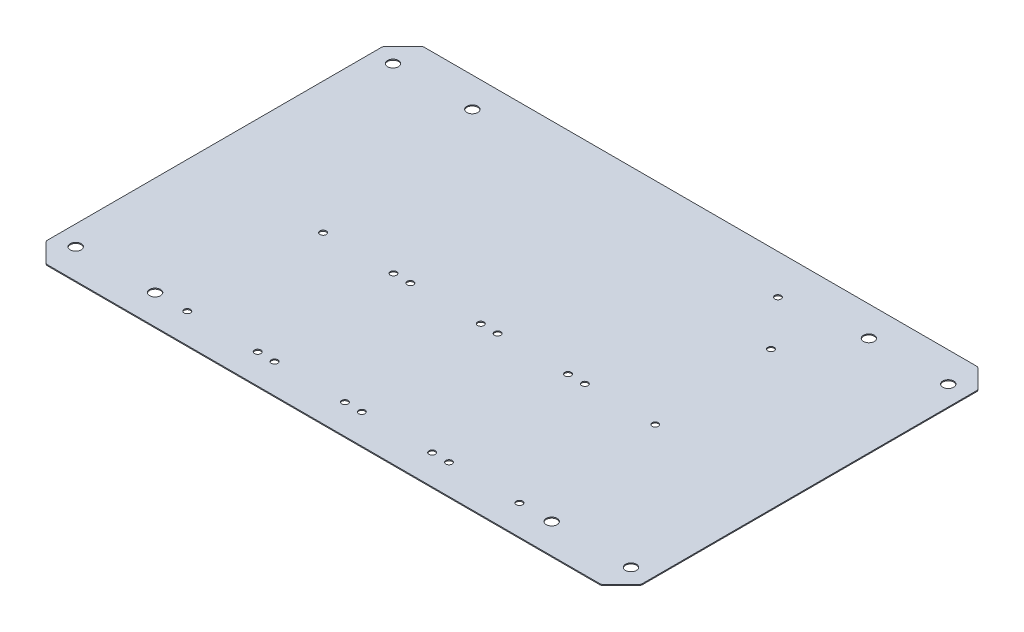
SolidWorks part; units mm, degrees
ref_plane "Plan de face" through (0, 0, 0) normal (0, 0, 1) x (1, 0, 0)
ref_plane "Plan de dessus" through (0, 0, 0) normal (0, 1, 0) x (1, 0, 0)
ref_plane "Plan de droite" through (0, 0, 0) normal (1, 0, 0) x (0, 0, -1)
sketch "Esquisse1" plane through (0, 0, 0) normal (0, 1, 0) x (1, 0, 0)
  line L1 (-150, -95) -> (150, -95)
  line L2 (-150, -95) -> (-150, 95)
  line L3 (-150, 95) -> (150, 95)
  line L4 (150, -95) -> (150, 95)
  line L5 (-150, -95) -> (150, 95) construction
  line L6 (-150, 95) -> (150, -95) construction
  point P0 (0, 0)
  dimension "D1" = 300
  dimension "D2" = 190
extrude "Boss.-Extru.1" add sketch "Esquisse1" along normal blind 0.5
chamfer "Chanfrein1" distance 10 angle 45 4 edges at (-150, 0.25, 95) (150, 0.25, 95) (150, 0.25, -95) (-150, 0.25, -95)
fillet "Congé1" radius 2 8 edges at (-150, 0.25, -85) (-140, 0.25, -95) (140, 0.25, -95) (150, 0.25, -85) (150, 0.25, 85) (140, 0.25, 95) (-140, 0.25, 95) (-150, 0.25, 85)
sketch "Esquisse2" plane through (0, 0, 0) normal (0, -1, 0) x (1, 0, 0)
  line L0 (-140, 80) -> (-100, 80) construction
  line L3 (-150, -84.1716) -> (-150, 84.1716) construction
  line L4 (-139.1716, 95) -> (139.1716, 95) construction
  circle A0 centre (-140, 80) radius 2.75
  circle A1 centre (-100, 80) radius 2.75
  point P4 (-120, 80)
  dimension "D1" = 5.5
  dimension "D2" = 40
  dimension "D3" = 10
  dimension "D4" = 15
extrude "Enlèv. mat.-Extru.1" cut sketch "Esquisse2" against normal through all
pattern_linear "Répétition linéaire1" count 2 spacing 240 along (1, 0, 0) count 2 spacing 160 along (0, 0, -1) of "Enlèv. mat.-Extru.1"
sketch "Esquisse3" plane through (0, 0.5, 0) normal (0, 1, 0) x (1, 0, 0)
  line L0 (-100, -80) -> (85, -80) construction
  line L1 (0, 0) -> (0, 50000) construction
  line L2 (0, 0) -> (50000, 0) construction
  circle A0 centre (-83.75, -80) radius 1.6
  circle A1 centre (-48.25, -80) radius 1.6
  circle A2 centre (-83.75, -11.5) radius 1.6
  circle A3 centre (-48.25, -11.5) radius 1.6
  dimension "D1" = 3.2
  dimension "D2" = 35.5
  dimension "D3" = 16.25
  dimension "D4" = 68.5
extrude "Enlèv. mat.-Extru.2" cut sketch "Esquisse3" against normal through all
pattern_linear "Répétition linéaire2" count 4 spacing 44 along (1, 0, 0) of "Enlèv. mat.-Extru.2"
sketch "Esquisse4" plane through (0, 0.5, 0) normal (0, 1, 0) x (1, 0, 0)
  circle A0 centre (59.1, 75) radius 1.6
  circle A1 centre (80, 50.6) radius 1.6
  circle A2 centre (100, 80) radius 2.75 construction
  circle A3 centre (100, 80) radius 2.75
  dimension "D1" = 3.2
  dimension "D4" = 20
  dimension "D2" = 24.4
  dimension "D3" = 20.9
  dimension "D5" = 5
extrude "Enlèv. mat.-Extru.3" cut sketch "Esquisse4" against normal blind 10
